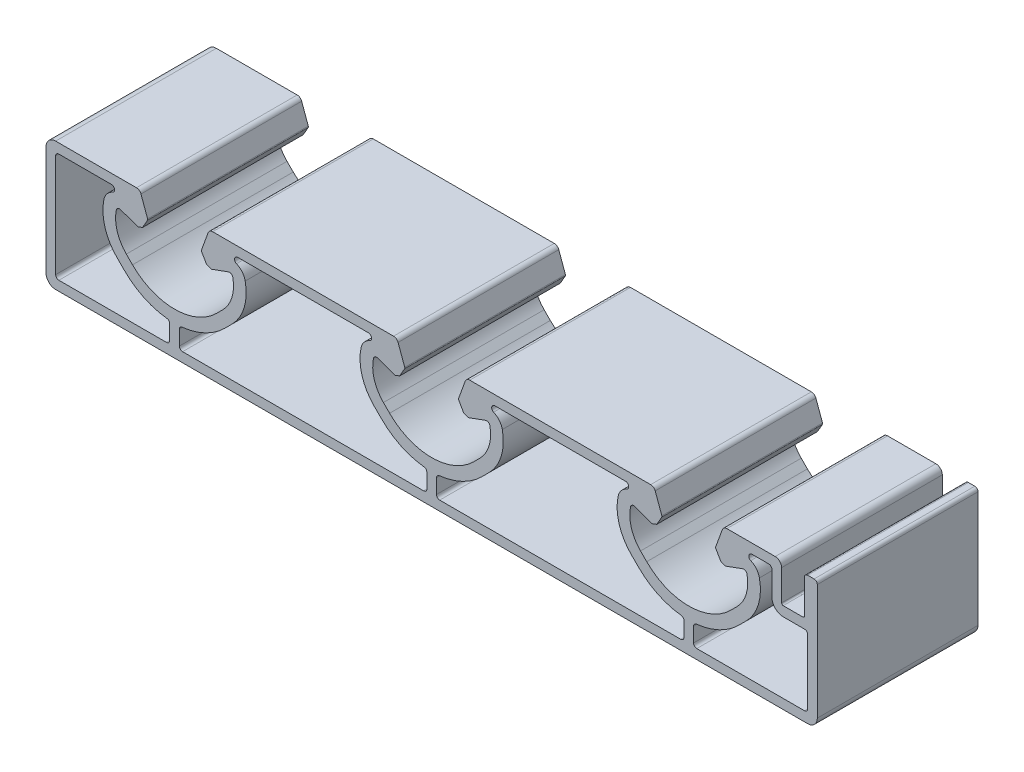
SolidWorks part; units mm, degrees
material "6005-T5"
ref_plane "Front" through (0, 0, 0) normal (0, 0, 1) x (1, 0, 0)
ref_plane "Top" through (0, 0, 0) normal (0, 1, 0) x (1, 0, 0)
ref_plane "Right" through (0, 0, 0) normal (1, 0, 0) x (0, 0, -1)
sketch "Sk Main Extrusion" plane through (0, 0, 0) normal (0, 0, 1) x (1, 0, 0)
  line L73 (-58.5, 8) -> (-58.5, -8)
  line L74 (-58, -8.5) -> (-41.25, -8.5)
  line L75 (-40.75, -8) -> (-40.75, -5.7322)
  line L76 (-47.8135, -2.0635) -> (-48.9493, -0.9278)
  line L77 (-49.8375, 8.5) -> (-58, 8.5)
  line L78 (-39.25, -5.7322) -> (-39.25, -8)
  line L79 (-38.75, -8.5) -> (-1.25, -8.5)
  line L80 (-0.75, -8) -> (-0.75, -5.7322)
  line L81 (-7.8135, -2.0635) -> (-8.9493, -0.9278)
  line L82 (-9.8375, 8.5) -> (-30.1625, 8.5)
  line L83 (-31.0507, -0.9278) -> (-32.1865, -2.0635)
  line L84 (8.9493, -0.9278) -> (7.8135, -2.0635)
  line L85 (0.75, -5.7322) -> (0.75, -8)
  line L86 (1.25, -8.5) -> (38.75, -8.5)
  line L87 (39.25, -8) -> (39.25, -5.7322)
  line L88 (32.1865, -2.0635) -> (31.0507, -0.9278)
  line L89 (30.1625, 8.5) -> (9.8375, 8.5)
  line L90 (-45.9268, 10) -> (-58.5, 10)
  line L91 (-60, 8.5) -> (-60, -8.5)
  line L92 (-58.5, -10) -> (58.5, -10)
  line L93 (60, -8.5) -> (60, 9.5)
  line L94 (59.5, 10) -> (58.5, 10)
  line L95 (58, 9.5) -> (58, 4.25)
  line L96 (57.75, 4) -> (54.694, 4)
  line L97 (54.444, 4.25) -> (54.444, 9)
  line L98 (53.444, 10) -> (45.9268, 10)
  line L99 (45.2221, 9.5065) -> (44.1901, 6.6712)
  line L100 (44.2085, 6.4607) -> (44.9876, 5.1113)
  line L101 (44.9876, 5.1113) -> (45.7185, 4.8453)
  line L102 (45.7185, 4.8453) -> (48.3962, 5.8198)
  line L103 (47.5042, 0.2727) -> (46.5407, -0.6907)
  line L104 (33.4593, -0.6907) -> (32.4958, 0.2727)
  line L105 (31.6038, 5.8198) -> (34.2815, 4.8453)
  line L106 (34.2815, 4.8453) -> (35.0124, 5.1113)
  line L107 (35.0124, 5.1113) -> (35.7915, 6.4607)
  line L108 (35.8099, 6.6712) -> (34.7779, 9.5065)
  line L109 (34.0732, 10) -> (5.9268, 10)
  line L110 (5.2221, 9.5065) -> (4.1901, 6.6712)
  line L111 (4.2085, 6.4607) -> (4.9876, 5.1113)
  line L112 (4.9876, 5.1113) -> (5.7185, 4.8453)
  line L113 (5.7185, 4.8453) -> (8.3962, 5.8198)
  line L114 (7.5042, 0.2727) -> (6.5407, -0.6907)
  line L115 (-6.5407, -0.6907) -> (-7.5042, 0.2727)
  line L116 (-8.3962, 5.8198) -> (-5.7185, 4.8453)
  line L117 (-5.7185, 4.8453) -> (-4.9876, 5.1113)
  line L118 (-4.9876, 5.1113) -> (-4.2085, 6.4607)
  line L119 (-4.1901, 6.6712) -> (-5.2221, 9.5065)
  line L120 (-5.9268, 10) -> (-34.0732, 10)
  line L121 (-34.7779, 9.5065) -> (-35.8099, 6.6712)
  line L122 (-35.7915, 6.4607) -> (-35.0124, 5.1113)
  line L123 (-35.0124, 5.1113) -> (-34.2815, 4.8453)
  line L124 (-34.2815, 4.8453) -> (-31.6038, 5.8198)
  line L125 (-32.4958, 0.2727) -> (-33.4593, -0.6907)
  line L126 (-46.5407, -0.6907) -> (-47.5042, 0.2727)
  line L127 (-48.3962, 5.8198) -> (-45.7185, 4.8453)
  line L128 (-45.7185, 4.8453) -> (-44.9876, 5.1113)
  line L129 (-44.9876, 5.1113) -> (-44.2085, 6.4607)
  line L130 (-44.1901, 6.6712) -> (-45.2221, 9.5065)
  line L131 (40.75, -5.7322) -> (40.75, -8)
  line L132 (41.25, -8.5) -> (58, -8.5)
  line L133 (58.5, -8) -> (58.5, 2)
  line L134 (58, 2.5) -> (54.694, 2.5)
  line L135 (52.944, 4.25) -> (52.944, 8)
  line L136 (52.444, 8.5) -> (49.8375, 8.5)
  line L137 (48.9493, -0.9278) -> (47.8135, -2.0635)
  arc A77 (-58, 8.5) -> (-58.5, 8) centre (-58, 8) ccw
  arc A78 (-58.5, -8) -> (-58, -8.5) centre (-58, -8) ccw
  arc A79 (-41.25, -8.5) -> (-40.75, -8) centre (-41.25, -8) ccw
  arc A80 (-40.75, -5.7322) -> (-41.1959, -5.2351) centre (-41.25, -5.7322) ccw
  arc A81 (-47.8135, -2.0635) -> (-41.1959, -5.2351) centre (-40, 5.75) ccw
  arc A82 (-50.9918, 5.8884) -> (-48.9493, -0.9278) centre (-43.646, 4.3755) ccw
  arc A83 (-49.6414, 7.5401) -> (-50.9918, 5.8884) centre (-48.7391, 5.4244) ccw
  arc A84 (-49.6414, 7.5401) -> (-49.8375, 8.5) centre (-49.8375, 8) ccw
  arc A85 (-38.8041, -5.2351) -> (-39.25, -5.7322) centre (-38.75, -5.7322) ccw
  arc A86 (-39.25, -8) -> (-38.75, -8.5) centre (-38.75, -8) ccw
  arc A87 (-1.25, -8.5) -> (-0.75, -8) centre (-1.25, -8) ccw
  arc A88 (-0.75, -5.7322) -> (-1.1959, -5.2351) centre (-1.25, -5.7322) ccw
  arc A89 (-7.8135, -2.0635) -> (-1.1959, -5.2351) centre (0, 5.75) ccw
  arc A90 (-10.9918, 5.8884) -> (-8.9493, -0.9278) centre (-3.646, 4.3755) ccw
  arc A91 (-9.6414, 7.5401) -> (-10.9918, 5.8884) centre (-8.7391, 5.4244) ccw
  arc A92 (-45.2221, 9.5065) -> (-45.9268, 10) centre (-45.9268, 9.25) ccw
  arc A93 (-58.5, 10) -> (-60, 8.5) centre (-58.5, 8.5) ccw
  arc A94 (-60, -8.5) -> (-58.5, -10) centre (-58.5, -8.5) ccw
  arc A95 (58.5, -10) -> (60, -8.5) centre (58.5, -8.5) ccw
  arc A96 (60, 9.5) -> (59.5, 10) centre (59.5, 9.5) ccw
  arc A97 (58.5, 10) -> (58, 9.5) centre (58.5, 9.5) ccw
  arc A98 (57.75, 4) -> (58, 4.25) centre (57.75, 4.25) ccw
  arc A99 (54.444, 4.25) -> (54.694, 4) centre (54.694, 4.25) ccw
  arc A100 (54.444, 9) -> (53.444, 10) centre (53.444, 9) ccw
  arc A101 (45.9268, 10) -> (45.2221, 9.5065) centre (45.9268, 9.25) ccw
  arc A102 (44.1901, 6.6712) -> (44.2085, 6.4607) centre (44.425, 6.5857) ccw
  arc A103 (49.057, 5.4507) -> (48.3962, 5.8198) centre (48.5672, 5.35) ccw
  arc A104 (47.5042, 0.2727) -> (49.057, 5.4507) centre (43.4737, 4.3032) ccw
  arc A105 (33.4593, -0.6907) -> (46.5407, -0.6907) centre (40, 5.85) ccw
  arc A106 (30.943, 5.4507) -> (32.4958, 0.2727) centre (36.5263, 4.3032) ccw
  arc A107 (31.6038, 5.8198) -> (30.943, 5.4507) centre (31.4328, 5.35) ccw
  arc A108 (35.7915, 6.4607) -> (35.8099, 6.6712) centre (35.575, 6.5857) ccw
  arc A109 (34.7779, 9.5065) -> (34.0732, 10) centre (34.0732, 9.25) ccw
  arc A110 (5.9268, 10) -> (5.2221, 9.5065) centre (5.9268, 9.25) ccw
  arc A111 (4.1901, 6.6712) -> (4.2085, 6.4607) centre (4.425, 6.5857) ccw
  arc A112 (9.057, 5.4507) -> (8.3962, 5.8198) centre (8.5672, 5.35) ccw
  arc A113 (7.5042, 0.2727) -> (9.057, 5.4507) centre (3.4737, 4.3032) ccw
  arc A114 (-6.5407, -0.6907) -> (6.5407, -0.6907) centre (0, 5.85) ccw
  arc A115 (-9.057, 5.4507) -> (-7.5042, 0.2727) centre (-3.4737, 4.3032) ccw
  arc A116 (-8.3962, 5.8198) -> (-9.057, 5.4507) centre (-8.5672, 5.35) ccw
  arc A117 (-4.2085, 6.4607) -> (-4.1901, 6.6712) centre (-4.425, 6.5857) ccw
  arc A118 (-5.2221, 9.5065) -> (-5.9268, 10) centre (-5.9268, 9.25) ccw
  arc A119 (-34.0732, 10) -> (-34.7779, 9.5065) centre (-34.0732, 9.25) ccw
  arc A120 (-35.8099, 6.6712) -> (-35.7915, 6.4607) centre (-35.575, 6.5857) ccw
  arc A121 (-30.943, 5.4507) -> (-31.6038, 5.8198) centre (-31.4328, 5.35) ccw
  arc A122 (-32.4958, 0.2727) -> (-30.943, 5.4507) centre (-36.5263, 4.3032) ccw
  arc A123 (-46.5407, -0.6907) -> (-33.4593, -0.6907) centre (-40, 5.85) ccw
  arc A124 (-49.057, 5.4507) -> (-47.5042, 0.2727) centre (-43.4737, 4.3032) ccw
  arc A125 (-48.3962, 5.8198) -> (-49.057, 5.4507) centre (-48.5672, 5.35) ccw
  arc A126 (-44.2085, 6.4607) -> (-44.1901, 6.6712) centre (-44.425, 6.5857) ccw
  arc A127 (-9.6414, 7.5401) -> (-9.8375, 8.5) centre (-9.8375, 8) ccw
  arc A128 (-30.1625, 8.5) -> (-30.3586, 7.5401) centre (-30.1625, 8) ccw
  arc A129 (-29.0082, 5.8884) -> (-30.3586, 7.5401) centre (-31.2609, 5.4244) ccw
  arc A130 (-31.0507, -0.9278) -> (-29.0082, 5.8884) centre (-36.354, 4.3755) ccw
  arc A131 (-38.8041, -5.2351) -> (-32.1865, -2.0635) centre (-40, 5.75) ccw
  arc A132 (9.8375, 8.5) -> (9.6414, 7.5401) centre (9.8375, 8) ccw
  arc A133 (10.9918, 5.8884) -> (9.6414, 7.5401) centre (8.7391, 5.4244) ccw
  arc A134 (8.9493, -0.9278) -> (10.9918, 5.8884) centre (3.646, 4.3755) ccw
  arc A135 (1.1959, -5.2351) -> (7.8135, -2.0635) centre (0, 5.75) ccw
  arc A136 (1.1959, -5.2351) -> (0.75, -5.7322) centre (1.25, -5.7322) ccw
  arc A137 (0.75, -8) -> (1.25, -8.5) centre (1.25, -8) ccw
  arc A138 (38.75, -8.5) -> (39.25, -8) centre (38.75, -8) ccw
  arc A139 (39.25, -5.7322) -> (38.8041, -5.2351) centre (38.75, -5.7322) ccw
  arc A140 (32.1865, -2.0635) -> (38.8041, -5.2351) centre (40, 5.75) ccw
  arc A141 (29.0082, 5.8884) -> (31.0507, -0.9278) centre (36.354, 4.3755) ccw
  arc A142 (30.3586, 7.5401) -> (29.0082, 5.8884) centre (31.2609, 5.4244) ccw
  arc A143 (30.3586, 7.5401) -> (30.1625, 8.5) centre (30.1625, 8) ccw
  arc A144 (41.1959, -5.2351) -> (40.75, -5.7322) centre (41.25, -5.7322) ccw
  arc A145 (40.75, -8) -> (41.25, -8.5) centre (41.25, -8) ccw
  arc A146 (58, -8.5) -> (58.5, -8) centre (58, -8) ccw
  arc A147 (58.5, 2) -> (58, 2.5) centre (58, 2) ccw
  arc A148 (52.944, 4.25) -> (54.694, 2.5) centre (54.694, 4.25) ccw
  arc A149 (52.944, 8) -> (52.444, 8.5) centre (52.444, 8) ccw
  arc A150 (49.8375, 8.5) -> (49.6414, 7.5401) centre (49.8375, 8) ccw
  arc A151 (50.9918, 5.8884) -> (49.6414, 7.5401) centre (48.7391, 5.4244) ccw
  arc A152 (48.9493, -0.9278) -> (50.9918, 5.8884) centre (43.646, 4.3755) ccw
  arc A153 (41.1959, -5.2351) -> (47.8135, -2.0635) centre (40, 5.75) ccw
  point P162 (0, 0)
extrude "Main Extrusion" add sketch "Sk Main Extrusion" against normal blind 25
sketch "Threaded Insert Mate Sketch" plane through (0, 0, 0) normal (0, 0, 1) x (1, 0, 0)
  line L0 (-5.9268, 10) -> (-34.0732, 10) construction
  line L2 (20, -8.5) -> (20, 8.5) construction
  line L3 (1.25, -8.5) -> (38.75, -8.5) construction
  line L4 (30.1625, 8.5) -> (9.8375, 8.5) construction
  line L5 (-20, -8.5) -> (-20, 8.5) construction
  line L10 (-9.8375, 8.5) -> (-30.1625, 8.5) construction
  line L11 (-38.75, -8.5) -> (-1.25, -8.5) construction
  circle A0 centre (0, 2.7) radius 5.6515
  circle A1 centre (40, 2.7) radius 5.6515
  circle A2 centre (-40, 2.7) radius 5.6515
  point P8 (0, 0)
  point P10 (0, 0)
  point P13 (0, 0)
  point P21 (0, 0)
  point P23 (0, 0)
  point P25 (0, 0)
  point P26 (0, 0)
  point P28 (0, 0)
  dimension "D2" = 11.303
  dimension "D1" = 7.3
equation "\"Weight kg\"= round ( \"SW-Mass\" , 2 )"
equation "\"Weight lbs\"= round ( \"SW-Mass\" * 2.2046 , 2 )"
equation "\"Length mm\"= round ( \"Length@Main Extrusion\" , 2 )"
equation "\"Length in\"= round ( \"Length@Main Extrusion\" / 25.4 , 3 )"
